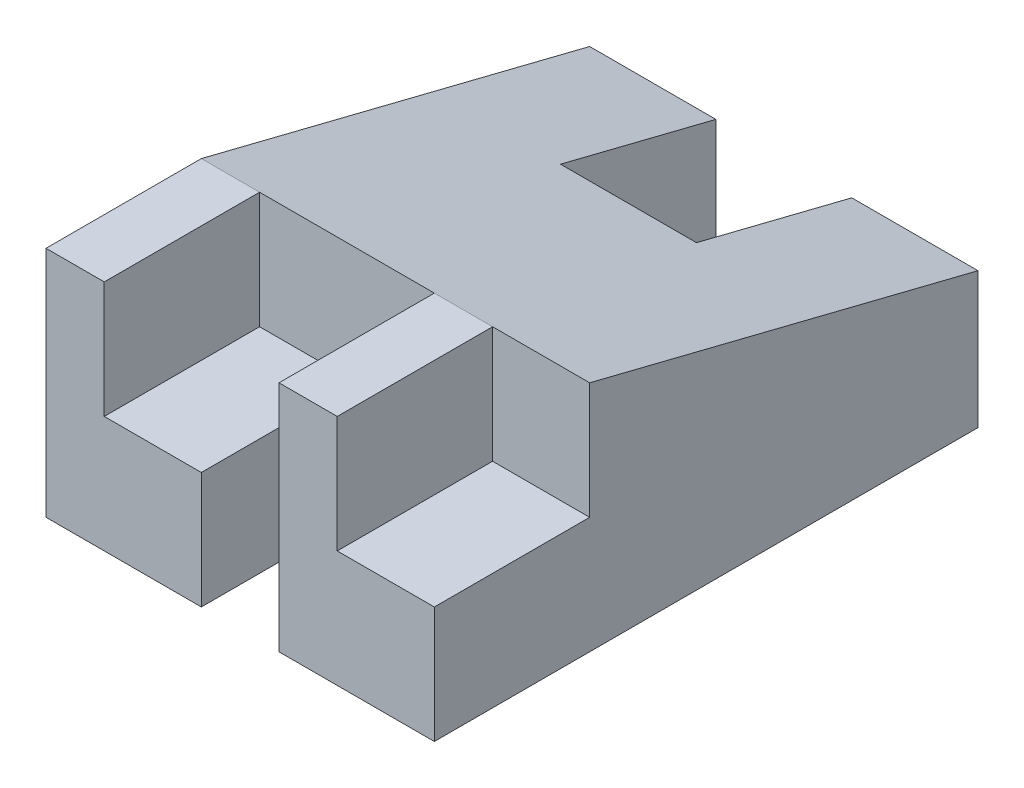
SolidWorks part; units mm, degrees
ref_plane "Front Plane" through (0, 0, 0) normal (0, 0, 1) x (1, 0, 0)
ref_plane "Top Plane" through (0, 0, 0) normal (0, 1, 0) x (1, 0, 0)
ref_plane "Right Plane" through (0, 0, 0) normal (1, 0, 0) x (0, 0, -1)
sketch "Sketch1" plane through (0, 0, 0) normal (1, 0, 0) x (0, 0, -1)
  line L0 (-52.0008, -26.4278) -> (36.8992, -26.4278)
  line L1 (36.8992, -26.4278) -> (36.8992, -4.2028)
  line L2 (36.8992, -4.2028) -> (-26.6008, 11.6722)
  line L3 (-52.0008, -26.4278) -> (-52.0008, 11.6722)
  line L6 (-26.6008, 11.6722) -> (-52.0008, 11.6722)
  dimension "D1" = 22.225
  dimension "D2" = 88.9
  dimension "D3" = 25.4
  dimension "D4" = 38.1
extrude "Boss-Extrude1" add sketch "Sketch1" along normal mid plane 63.5
sketch "Sketch2" plane through (0, 11.6722, 0) normal (0, 1, 0) x (1, 0, 0)
  line L1 (31.75, -52.0008) -> (-31.75, -52.0008) construction
  line L2 (-6.35, -52.0008) -> (6.35, -52.0008)
  line L3 (-6.35, -52.0008) -> (-6.35, -26.6008)
  line L4 (-6.35, -26.6008) -> (6.35, -26.6008)
  line L5 (6.35, -52.0008) -> (6.35, -26.6008)
  line L6 (31.75, -26.6008) -> (-31.75, -26.6008) construction
  line L9 (0, -20.955) -> (0, 20.955) construction
  point P9 (0, -52.0008)
  dimension "D1" = 12.7
extrude "Cut-Extrude1" cut sketch "Sketch2" against normal blind 63.5
sketch "Sketch3" plane through (0, 11.6722, 0) normal (0, 1, 0) x (1, 0, 0)
  line L0 (31.75, -52.0008) -> (6.35, -52.0008) construction
  line L1 (31.75, -26.6008) -> (15.875, -26.6008)
  line L2 (31.75, -26.6008) -> (31.75, -52.0008)
  line L3 (31.75, -52.0008) -> (15.875, -52.0008)
  line L4 (15.875, -26.6008) -> (15.875, -52.0008)
  line L5 (6.35, -26.6008) -> (-6.35, -26.6008) construction
  line L6 (-6.35, -26.6008) -> (-31.75, -26.6008) construction
  line L7 (-6.35, -52.0008) -> (-22.225, -52.0008)
  line L8 (-6.35, -52.0008) -> (-6.35, -26.6008)
  line L9 (-6.35, -26.6008) -> (-22.225, -26.6008)
  line L10 (-22.225, -52.0008) -> (-22.225, -26.6008)
  dimension "D1" = 15.875
  dimension "D2" = 15.875
extrude "Cut-Extrude2" cut sketch "Sketch3" against normal blind 19.05
sketch "Sketch4" plane through (0, -26.4278, 0) normal (0, -1, 0) x (1, 0, 0)
  line L0 (31.75, -36.8992) -> (-31.75, -36.8992) construction
  line L1 (11.1125, -36.8992) -> (-11.1125, -36.8992)
  line L2 (11.1125, -36.8992) -> (11.1125, -11.4992)
  line L3 (11.1125, -11.4992) -> (-11.1125, -11.4992)
  line L4 (-11.1125, -36.8992) -> (-11.1125, -11.4992)
  line L6 (31.75, 52.0008) -> (31.75, -36.8992) construction
  point P6 (0, -36.8992)
  point P7 (0, -36.8992)
  dimension "D1" = 20.6375
  dimension "D2" = 25.4
extrude "Cut-Extrude3" cut sketch "Sketch4" against normal through all
